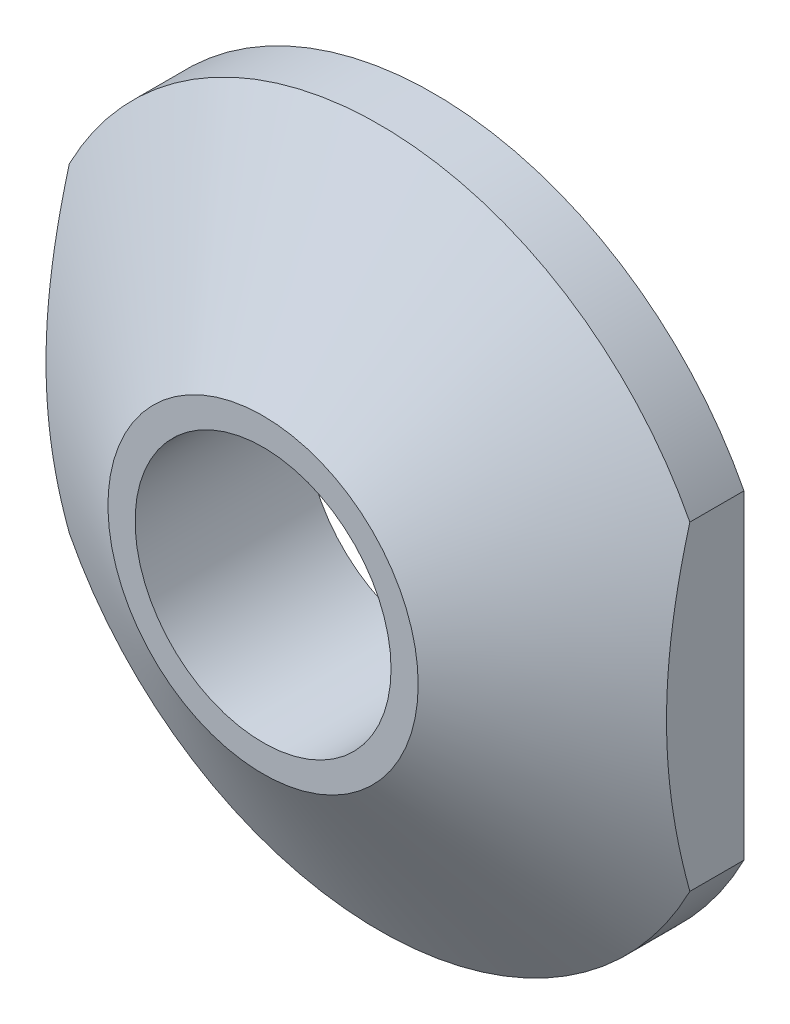
SolidWorks part; units mm, degrees
ref_plane "Front Plane" through (0, 0, 0) normal (0, 0, 1) x (1, 0, 0)
ref_plane "Top Plane" through (0, 0, 0) normal (0, 1, 0) x (1, 0, 0)
ref_plane "Right Plane" through (0, 0, 0) normal (1, 0, 0) x (0, 0, -1)
sketch "Sketch2" plane through (0, 0, 0) normal (0, 1, 0) x (1, 0, 0)
  line L0 (2, 0) -> (4.5, 1.5022)
  line L1 (4.5, 1.5022) -> (4.5, 2.2)
  line L2 (4.5, 2.2) -> (1.65, 2.2)
  line L4 (0, 0) -> (0, 2.2) construction
  line L5 (2, 0) -> (1.65, 0)
  line L6 (1.65, 0) -> (1.65, 2.2)
  dimension "D1" = 31
  dimension "D2" = 4
  dimension "D3" = 2.2
  dimension "D4" = 9
  dimension "D5" = 3.3
revolve "Revolve1" add sketch "Sketch2" angle 360 about L4
cosmetic thread "Cosmetic Thread1" parameters "D1"=2, "D2"=4
sketch "Sketch3" plane through (0, 0, -2.2) normal (0, 0, -1) x (-1, 0, 0)
  line L1 (-4, 3.4599) -> (-6.4342, 3.4599)
  line L2 (-4, 3.4599) -> (-4, -3.7049)
  line L3 (-4, -3.7049) -> (-6.4342, -3.7049)
  line L4 (-6.4342, 3.4599) -> (-6.4342, -3.7049)
  dimension "D1" = 4
extrude "Cut-Extrude1" cut sketch "Sketch3" against normal through all
mirror "Mirror1" about plane through (0, 0, 0) normal (1, 0, 0) of "Cut-Extrude1"
